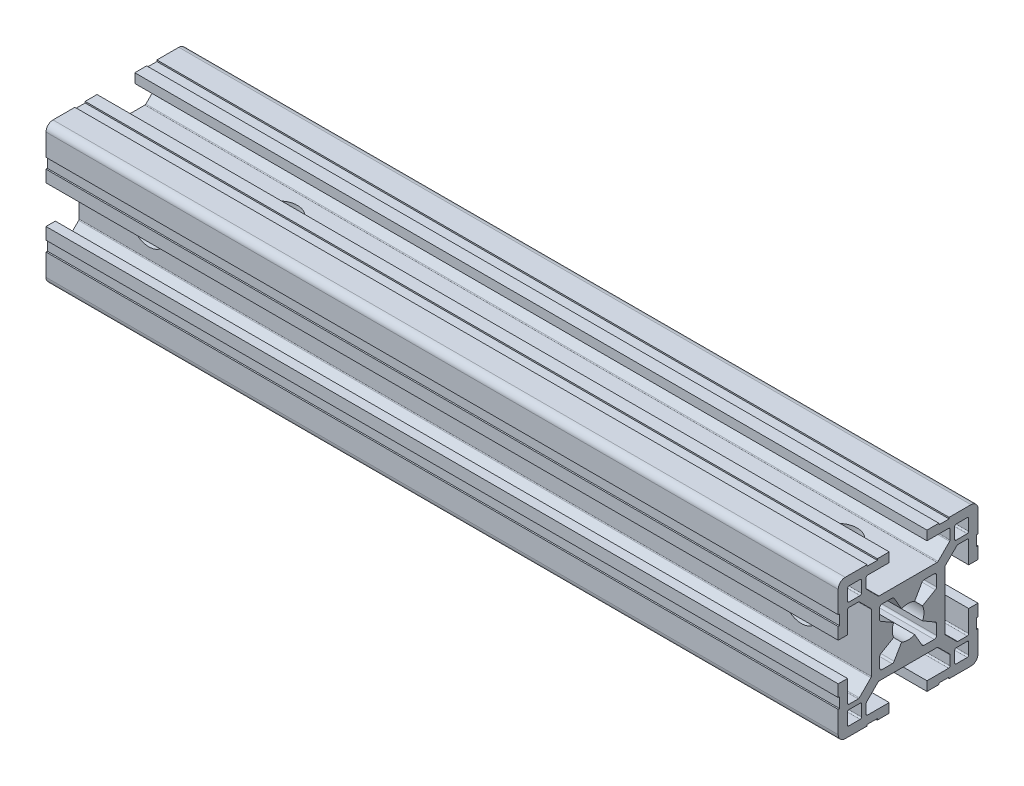
SolidWorks part; units mm, degrees
material "6063-T5"
ref_plane "Plano frontal" through (0, 0, 0) normal (0, 0, 1) x (1, 0, 0)
ref_plane "Plano superior" through (0, 0, 0) normal (0, 1, 0) x (1, 0, 0)
ref_plane "Plano direito" through (0, 0, 0) normal (1, 0, 0) x (0, 0, -1)
sketch "Esboço1" plane through (0, 0, 0) normal (0, 0, 1) x (1, 0, 0)
  line L0 (0, 0) -> (170, 0)
  dimension "D1" = 170
other "Quadrado PF30-11 - PERFIL 3030 CENTRO M8(1)"
ref_plane "Plano1" through (0, 0, 0) normal (1, 0, 0) x (0, 1, 0)
sketch "Sketch1" plane through (0, 0, 0) normal (1, 0, 0) x (0, 1, 0)
  line L0 (-6.1, -3.4254) -> (-6.1, -5.6)
  line L1 (-5.6, -6.1) -> (-3.4254, -6.1)
  line L2 (3.4254, -6.1) -> (5.6, -6.1)
  line L3 (6.1, -5.6) -> (6.1, -3.4254)
  line L4 (6.1, 3.4254) -> (6.1, 5.6)
  line L5 (5.6, 6.1) -> (3.4254, 6.1)
  line L6 (-3.4254, 6.1) -> (-5.6, 6.1)
  line L7 (-6.1, 5.6) -> (-6.1, 3.4254)
  line L8 (15, 6.6) -> (14.7, 6.6)
  line L9 (5.85, -2.9924) -> (3.097, -1.403)
  line L10 (10, 12.7) -> (10, 10.3)
  line L11 (13, -12.7) -> (13, -10.3)
  line L12 (-10.3, -10) -> (-12.7, -10)
  line L13 (-13, 12.7) -> (-13, 10.3)
  line L14 (3.097, 1.403) -> (5.85, 2.9924)
  line L15 (2.9924, 5.85) -> (1.403, 3.097)
  line L16 (-1.403, 3.097) -> (-2.9924, 5.85)
  line L17 (-5.85, 2.9924) -> (-3.097, 1.403)
  line L18 (-3.097, -1.403) -> (-5.85, -2.9924)
  line L19 (-2.9924, -5.85) -> (-1.403, -3.097)
  line L20 (1.403, -3.097) -> (2.9924, -5.85)
  line L21 (10.3, 10) -> (12.7, 10)
  line L22 (13, 10.3) -> (13, 12.7)
  line L23 (12.7, 13) -> (10.3, 13)
  line L24 (12.7, -10) -> (10.3, -10)
  line L25 (10, -10.3) -> (10, -12.7)
  line L26 (10.3, -13) -> (12.7, -13)
  line L27 (-13, -10.3) -> (-13, -12.7)
  line L28 (-12.7, -13) -> (-10.3, -13)
  line L29 (-10, -12.7) -> (-10, -10.3)
  line L30 (-12.7, 10) -> (-10.3, 10)
  line L31 (-10, 10.3) -> (-10, 12.7)
  line L32 (-10.3, 13) -> (-12.7, 13)
  line L33 (15, 4.05) -> (15, 6.6)
  line L34 (13, 4.05) -> (15, 4.05)
  line L35 (13, 8.7) -> (13, 4.05)
  line L36 (10.6799, 9) -> (12.7, 9)
  line L37 (7.9879, 6.4322) -> (10.4678, 8.9121)
  line L38 (7.9, -6.2201) -> (7.9, 6.2201)
  line L39 (10.4678, -8.9121) -> (7.9879, -6.4322)
  line L40 (12.7, -9) -> (10.6799, -9)
  line L41 (13, -4.05) -> (13, -8.7)
  line L42 (15, -4.05) -> (13, -4.05)
  line L43 (15, -6.6) -> (15, -4.05)
  line L44 (14.7, -6.6) -> (15, -6.6)
  line L45 (14.7, -8.8) -> (14.7, -6.6)
  line L46 (15, -8.8) -> (14.7, -8.8)
  line L47 (15, -13.5) -> (15, -8.8)
  line L48 (8.8, -15) -> (13.5, -15)
  line L49 (8.8, -14.7) -> (8.8, -15)
  line L50 (6.6, -14.7) -> (8.8, -14.7)
  line L51 (6.6, -15) -> (6.6, -14.7)
  line L52 (4.05, -15) -> (6.6, -15)
  line L53 (4.05, -13) -> (4.05, -15)
  line L54 (8.7, -13) -> (4.05, -13)
  line L55 (9, -10.6799) -> (9, -12.7)
  line L56 (6.4322, -7.9879) -> (8.9121, -10.4678)
  line L57 (-6.2201, -7.9) -> (6.2201, -7.9)
  line L58 (-8.9121, -10.4678) -> (-6.4322, -7.9879)
  line L59 (-9, -12.7) -> (-9, -10.6799)
  line L60 (-4.05, -13) -> (-8.7, -13)
  line L61 (-4.05, -15) -> (-4.05, -13)
  line L62 (-6.6, -15) -> (-4.05, -15)
  line L63 (-6.6, -14.7) -> (-6.6, -15)
  line L64 (-8.8, -14.7) -> (-6.6, -14.7)
  line L65 (-8.8, -15) -> (-8.8, -14.7)
  line L66 (-13.5, -15) -> (-8.8, -15)
  line L67 (-15, -8.8) -> (-15, -13.5)
  line L68 (-14.7, -8.8) -> (-15, -8.8)
  line L69 (-14.7, -6.6) -> (-14.7, -8.8)
  line L70 (-15, -6.6) -> (-14.7, -6.6)
  line L71 (-15, -4.05) -> (-15, -6.6)
  line L72 (-13, -4.05) -> (-15, -4.05)
  line L73 (-13, -8.7) -> (-13, -4.05)
  line L74 (-10.6799, -9) -> (-12.7, -9)
  line L75 (-7.9879, -6.4322) -> (-10.4678, -8.9121)
  line L76 (-7.9, 6.2201) -> (-7.9, -6.2201)
  line L77 (-10.4678, 8.9121) -> (-7.9879, 6.4322)
  line L78 (-12.7, 9) -> (-10.6799, 9)
  line L79 (-13, 4.05) -> (-13, 8.7)
  line L80 (-15, 4.05) -> (-13, 4.05)
  line L81 (-15, 6.6) -> (-15, 4.05)
  line L82 (-14.7, 6.6) -> (-15, 6.6)
  line L83 (-14.7, 8.8) -> (-14.7, 6.6)
  line L84 (-15, 8.8) -> (-14.7, 8.8)
  line L85 (-15, 13.5) -> (-15, 8.8)
  line L86 (-8.8, 15) -> (-13.5, 15)
  line L87 (-8.8, 14.7) -> (-8.8, 15)
  line L88 (-6.6, 14.7) -> (-8.8, 14.7)
  line L89 (-6.6, 15) -> (-6.6, 14.7)
  line L90 (-4.05, 15) -> (-6.6, 15)
  line L91 (-4.05, 13) -> (-4.05, 15)
  line L92 (-8.7, 13) -> (-4.05, 13)
  line L93 (-9, 10.6799) -> (-9, 12.7)
  line L94 (-6.4322, 7.9879) -> (-8.9121, 10.4678)
  line L95 (6.2201, 7.9) -> (-6.2201, 7.9)
  line L96 (8.9121, 10.4678) -> (6.4322, 7.9879)
  line L97 (9, 12.7) -> (9, 10.6799)
  line L98 (4.05, 13) -> (8.7, 13)
  line L99 (4.05, 15) -> (4.05, 13)
  line L100 (6.6, 15) -> (4.05, 15)
  line L101 (6.6, 14.7) -> (6.6, 15)
  line L102 (8.8, 14.7) -> (6.6, 14.7)
  line L103 (8.8, 15) -> (8.8, 14.7)
  line L104 (13.5, 15) -> (8.8, 15)
  line L105 (15, 8.8) -> (15, 13.5)
  line L106 (14.7, 8.8) -> (15, 8.8)
  line L107 (14.7, 6.6) -> (14.7, 8.8)
  arc A0 (-5.85, -2.9924) -> (-6.1, -3.4254) centre (-5.6, -3.4254) ccw
  arc A1 (-6.1, -5.6) -> (-5.6, -6.1) centre (-5.6, -5.6) ccw
  arc A2 (-3.4254, -6.1) -> (-2.9924, -5.85) centre (-3.4254, -5.6) ccw
  arc A3 (2.9924, -5.85) -> (3.4254, -6.1) centre (3.4254, -5.6) ccw
  arc A4 (5.6, -6.1) -> (6.1, -5.6) centre (5.6, -5.6) ccw
  arc A5 (6.1, -3.4254) -> (5.85, -2.9924) centre (5.6, -3.4254) ccw
  arc A6 (5.85, 2.9924) -> (6.1, 3.4254) centre (5.6, 3.4254) ccw
  arc A7 (6.1, 5.6) -> (5.6, 6.1) centre (5.6, 5.6) ccw
  arc A8 (3.4254, 6.1) -> (2.9924, 5.85) centre (3.4254, 5.6) ccw
  arc A9 (-2.9924, 5.85) -> (-3.4254, 6.1) centre (-3.4254, 5.6) ccw
  arc A10 (-5.6, 6.1) -> (-6.1, 5.6) centre (-5.6, 5.6) ccw
  arc A11 (-6.1, 3.4254) -> (-5.85, 2.9924) centre (-5.6, 3.4254) ccw
  arc A12 (3.097, -1.403) -> (3.097, 1.403) centre (0, 0) ccw
  arc A13 (1.403, 3.097) -> (-1.403, 3.097) centre (0, 0) ccw
  arc A14 (-3.097, 1.403) -> (-3.097, -1.403) centre (0, 0) ccw
  arc A15 (-1.403, -3.097) -> (1.403, -3.097) centre (0, 0) ccw
  arc A16 (10, 10.3) -> (10.3, 10) centre (10.3, 10.3) ccw
  arc A17 (12.7, 10) -> (13, 10.3) centre (12.7, 10.3) ccw
  arc A18 (13, 12.7) -> (12.7, 13) centre (12.7, 12.7) ccw
  arc A19 (10.3, 13) -> (10, 12.7) centre (10.3, 12.7) ccw
  arc A20 (13, -10.3) -> (12.7, -10) centre (12.7, -10.3) ccw
  arc A21 (10.3, -10) -> (10, -10.3) centre (10.3, -10.3) ccw
  arc A22 (10, -12.7) -> (10.3, -13) centre (10.3, -12.7) ccw
  arc A23 (12.7, -13) -> (13, -12.7) centre (12.7, -12.7) ccw
  arc A24 (-12.7, -10) -> (-13, -10.3) centre (-12.7, -10.3) ccw
  arc A25 (-13, -12.7) -> (-12.7, -13) centre (-12.7, -12.7) ccw
  arc A26 (-10.3, -13) -> (-10, -12.7) centre (-10.3, -12.7) ccw
  arc A27 (-10, -10.3) -> (-10.3, -10) centre (-10.3, -10.3) ccw
  arc A28 (-13, 10.3) -> (-12.7, 10) centre (-12.7, 10.3) ccw
  arc A29 (-10.3, 10) -> (-10, 10.3) centre (-10.3, 10.3) ccw
  arc A30 (-10, 12.7) -> (-10.3, 13) centre (-10.3, 12.7) ccw
  arc A31 (-12.7, 13) -> (-13, 12.7) centre (-12.7, 12.7) ccw
  arc A32 (13, 8.7) -> (12.7, 9) centre (12.7, 8.7) ccw
  arc A33 (10.6799, 9) -> (10.4678, 8.9121) centre (10.6799, 8.7) ccw
  arc A34 (7.9879, 6.4322) -> (7.9, 6.2201) centre (8.2, 6.2201) ccw
  arc A35 (7.9, -6.2201) -> (7.9879, -6.4322) centre (8.2, -6.2201) ccw
  arc A36 (10.4678, -8.9121) -> (10.6799, -9) centre (10.6799, -8.7) ccw
  arc A37 (12.7, -9) -> (13, -8.7) centre (12.7, -8.7) ccw
  arc A38 (13.5, -15) -> (15, -13.5) centre (13.5, -13.5) ccw
  arc A39 (8.7, -13) -> (9, -12.7) centre (8.7, -12.7) ccw
  arc A40 (9, -10.6799) -> (8.9121, -10.4678) centre (8.7, -10.6799) ccw
  arc A41 (6.4322, -7.9879) -> (6.2201, -7.9) centre (6.2201, -8.2) ccw
  arc A42 (-6.2201, -7.9) -> (-6.4322, -7.9879) centre (-6.2201, -8.2) ccw
  arc A43 (-8.9121, -10.4678) -> (-9, -10.6799) centre (-8.7, -10.6799) ccw
  arc A44 (-9, -12.7) -> (-8.7, -13) centre (-8.7, -12.7) ccw
  arc A45 (-15, -13.5) -> (-13.5, -15) centre (-13.5, -13.5) ccw
  arc A46 (-13, -8.7) -> (-12.7, -9) centre (-12.7, -8.7) ccw
  arc A47 (-10.6799, -9) -> (-10.4678, -8.9121) centre (-10.6799, -8.7) ccw
  arc A48 (-7.9879, -6.4322) -> (-7.9, -6.2201) centre (-8.2, -6.2201) ccw
  arc A49 (-7.9, 6.2201) -> (-7.9879, 6.4322) centre (-8.2, 6.2201) ccw
  arc A50 (-10.4678, 8.9121) -> (-10.6799, 9) centre (-10.6799, 8.7) ccw
  arc A51 (-12.7, 9) -> (-13, 8.7) centre (-12.7, 8.7) ccw
  arc A52 (-13.5, 15) -> (-15, 13.5) centre (-13.5, 13.5) ccw
  arc A53 (-8.7, 13) -> (-9, 12.7) centre (-8.7, 12.7) ccw
  arc A54 (-9, 10.6799) -> (-8.9121, 10.4678) centre (-8.7, 10.6799) ccw
  arc A55 (-6.4322, 7.9879) -> (-6.2201, 7.9) centre (-6.2201, 8.2) ccw
  arc A56 (6.2201, 7.9) -> (6.4322, 7.9879) centre (6.2201, 8.2) ccw
  arc A57 (8.9121, 10.4678) -> (9, 10.6799) centre (8.7, 10.6799) ccw
  arc A58 (9, 12.7) -> (8.7, 13) centre (8.7, 12.7) ccw
  arc A59 (15, 13.5) -> (13.5, 15) centre (13.5, 13.5) ccw
  point P1 (0, 0)
  point P2 (0, 0)
  point P3 (-15, -15)
  point P4 (0, -15)
  point P5 (-15, 0)
  point P230 (-15, 15)
  point P231 (0, 15)
  point P232 (15, 15)
  point P233 (15, 0)
  point P234 (15, -15)
  point P235 (0, -15)
  point P236 (-15, -15)
  point P237 (-15, 0)
  point P238 (0, 0)
  point P239 (0, 0)
sketch "Esboço3" plane through (0, 0, 7.9) normal (0, 0, 1) x (1, 0, 0)
  line L0 (0, 15) -> (17.3205, -15)
  line L1 (170, -15) -> (0, -15) construction
  line L2 (17.3205, -15) -> (0, -15)
  line L3 (0, -15) -> (0, 15)
  dimension "D1" = 30
extrude "Corte-extrusão2" [suppressed] cut sketch "Esboço3" against normal through all both and the other way through all
sketch "Esboço5" plane through (0, 0, 7.9) normal (0, 0, 1) x (1, 0, 0)
  line L3 (0, -6.2201) -> (0, 6.2201) construction
  circle A0 centre (15, 0) radius 3.9
  circle A1 centre (155, 0) radius 3.9
  arc A2 (158.097, -1.403) -> (158.097, 1.403) centre (155, 0) ccw construction
  dimension "D1" = 7.8
  dimension "D2" = 15
extrude "Corte-extrusão3" cut sketch "Esboço5" against normal through all
sketch "Esboço6" plane through (0, -7.9, 0) normal (0, -1, 0) x (1, 0, 0)
  line L2 (170, 6.2201) -> (170, -6.2201) construction
  line L3 (170, -4.05) -> (0, -4.05) construction
  line L4 (170, 4.05) -> (0, 4.05) construction
  circle A1 centre (155, 0) radius 4.05
  circle A3 centre (35, 0) radius 3.95
  point P11 (0, 0)
  dimension "D1" = 7.9
  dimension "D2" = 35
  dimension "D3" = 15
extrude "Corte-extrusão4" cut sketch "Esboço6" against normal through all
